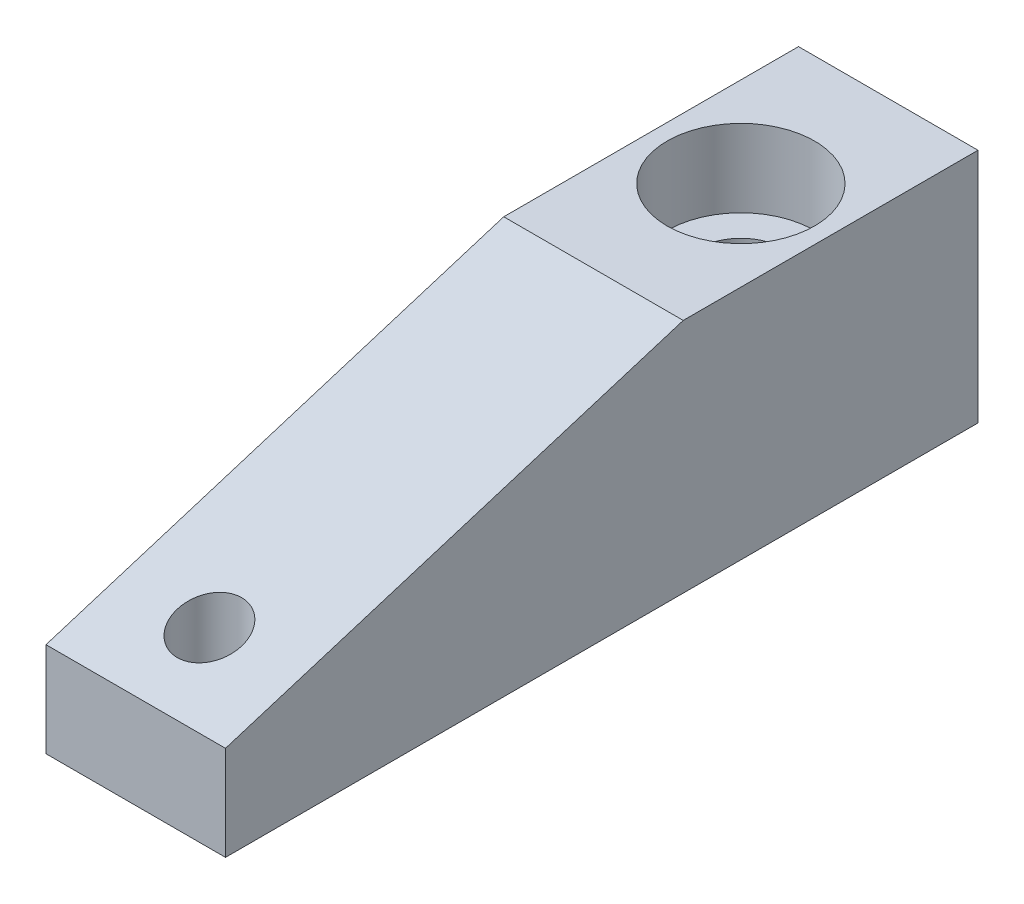
SolidWorks part; units mm, degrees
material "Alloy Steel"
ref_plane "Front Plane" through (0, 0, 0) normal (0, 0, 1) x (1, 0, 0)
ref_plane "Top Plane" through (0, 0, 0) normal (0, 1, 0) x (1, 0, 0)
ref_plane "Right Plane" through (0, 0, 0) normal (1, 0, 0) x (0, 0, -1)
sketch "Sketch1" plane through (0, 0, 0) normal (0, 1, 0) x (1, 0, 0)
  line L1 (0, 0) -> (9.652, 0)
  line L2 (0, 0) -> (0, -40.4622)
  line L3 (0, -40.4622) -> (9.652, -40.4622)
  line L4 (9.652, 0) -> (9.652, -40.4622)
  dimension "D1" = 9.652
  dimension "D2" = 40.4622
extrude "Extrude1" add sketch "Sketch1" along normal blind 12.7
ref_plane "Plane1" through (4.826, 0, 0) normal (1, 0, 0) x (0, 0, -1)
sketch "Sketch3" plane through (4.826, 0, 0) normal (1, 0, 0) x (0, 0, -1)
  line L0 (-7.9248, 31.6794) -> (-7.9248, -3.5955) construction
  line L1 (0, 12.7) -> (0, 0) construction
  line L2 (-11.8872, 12.7) -> (-11.8872, 8.5344)
  line L3 (-40.4622, 12.7) -> (0, 12.7) construction
  line L4 (-11.8872, 8.5344) -> (-10.2108, 8.5344)
  line L5 (-10.2108, 8.5344) -> (-10.2108, 6.6548)
  line L6 (-10.2108, 6.6548) -> (-10.6293, 6.6548)
  line L7 (-10.6293, 6.6548) -> (-11.0363, 0)
  line L8 (-40.4622, 0) -> (0, 0) construction
  line L9 (-11.0363, 0) -> (-7.9248, 0)
  line L10 (-7.9248, 0) -> (-7.9248, 12.7)
  line L11 (-7.9248, 12.7) -> (-11.8872, 12.7)
  dimension "D1" = 7.9248
  dimension "D2" = 7.9248
  dimension "D3" = 4.1656
  dimension "D4" = 4.572
  dimension "D5" = 6.6548
  dimension "D6" = 3.5
  dimension "D7" = 6.223
revolve "Cut-Revolve1" cut sketch "Sketch3" angle 360 about L0
fillet "Fillet1" radius 0.127 1 edges at (4.826, 6.6548, 10.6293)
sketch "Sketch4" plane through (9.652, 0, 0) normal (1, 0, 0) x (0, 0, -1)
  line L0 (-40.4622, 5.08) -> (-40.4622, 12.7)
  line L1 (-40.4622, 12.7) -> (0, 12.7) construction
  line L2 (-40.4622, 12.7) -> (-15.8496, 12.7)
  line L3 (-40.4622, 5.08) -> (-15.8496, 12.7)
  line L4 (-40.4622, 12.7) -> (-40.4622, 0) construction
  line L6 (-7.9248, 8.5344) -> (-7.9248, 12.7) construction
  line L7 (-40.4622, 0) -> (0, 0) construction
  dimension "D1" = 7.9248
  dimension "D2" = 5.08
extrude "Cut-Extrude1" cut sketch "Sketch4" against normal through all
sketch "Sketch5" plane through (0, 0, 0) normal (0, -1, 0) x (1, 0, 0)
  circle A0 centre (4.826, 36.4998) radius 1.7272
  dimension "D1" = 3.4544
  dimension "D2" = 28.575
extrude "Cut-Extrude2" cut sketch "Sketch5" against normal through all
